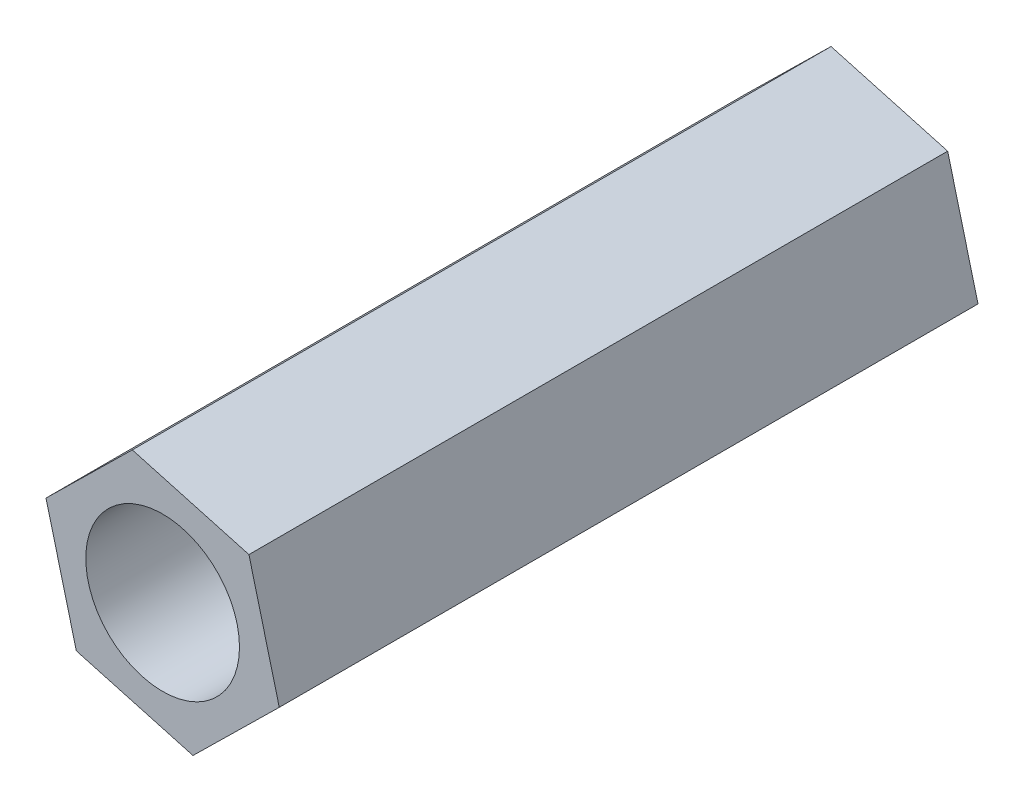
SolidWorks part; units mm, degrees
ref_plane "前视基准面" through (0, 0, 0) normal (0, 0, 1) x (1, 0, 0)
ref_plane "上视基准面" through (0, 0, 0) normal (0, 1, 0) x (1, 0, 0)
ref_plane "右视基准面" through (0, 0, 0) normal (1, 0, 0) x (0, 0, -1)
sketch "草图1" plane through (0, 0, 0) normal (0, 0, 1) x (1, 0, 0)
  line L1 (1.8527, 1.8214) -> (-0.6511, 2.5152)
  line L2 (-0.6511, 2.5152) -> (-2.5037, 0.6938)
  line L3 (-2.5037, 0.6938) -> (-1.8527, -1.8214)
  line L4 (-1.8527, -1.8214) -> (0.6511, -2.5152)
  line L5 (0.6511, -2.5152) -> (2.5037, -0.6938)
  line L6 (2.5037, -0.6938) -> (1.8527, 1.8214)
  circle A0 centre (0, 0) radius 1.65
  circle A1 centre (0, 0) radius 2.25 construction
  dimension "D2" = 3.3
  dimension "D1" = 4.5
extrude "凸台-拉伸1" add sketch "草图1" along normal blind 15
